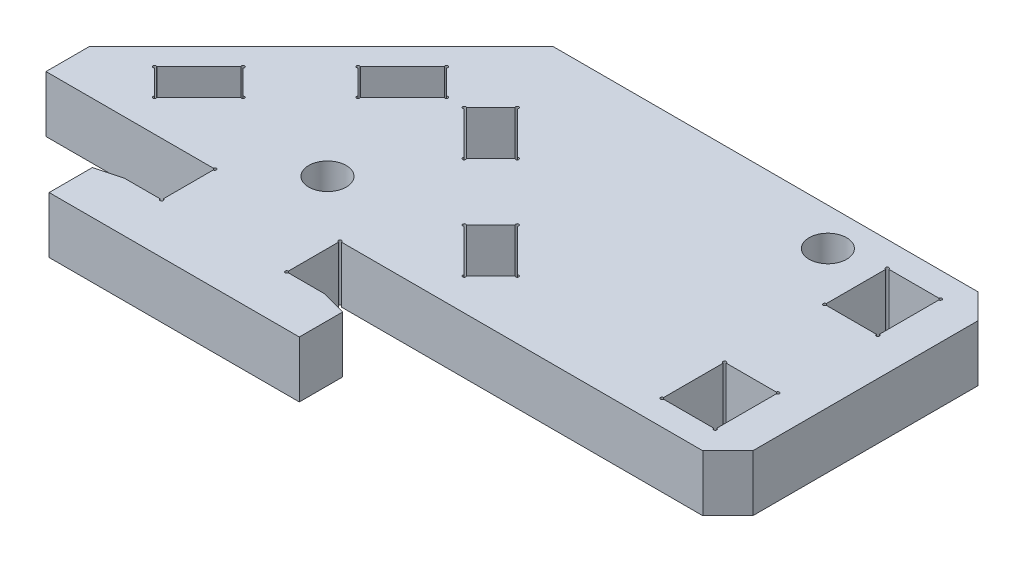
SolidWorks part; units mm, degrees
ref_plane "Front Plane" through (0, 0, 0) normal (0, 0, 1) x (1, 0, 0)
ref_plane "Top Plane" through (0, 0, 0) normal (0, 1, 0) x (1, 0, 0)
ref_plane "Right Plane" through (0, 0, 0) normal (1, 0, 0) x (0, 0, -1)
sketch "Sketch1" plane through (0, 0, 0) normal (0, 1, 0) x (1, 0, 0)
  line L0 (-18.5, -18.5) -> (0, 0)
  line L1 (0, 0) -> (36, 0)
  line L2 (36, 0) -> (36, -22)
  line L3 (36, -22) -> (-18.5, -22)
  line L4 (-18.5, -18.5) -> (-18.5, -22)
  dimension "D1" = 22
  dimension "D2" = 45
  dimension "D3" = 36
  dimension "D4" = 3.5
extrude "Boss-Extrude1" add sketch "Sketch1" along normal blind 4.5
sketch "Sketch2" plane through (0, 4.5, 0) normal (0, 1, 0) x (1, 0, 0)
  line L0 (-6.364, -9.1924) -> (-2.8284, -5.6569)
  line L1 (-6.364, -9.1924) -> (-4.2426, -11.3137)
  line L2 (-2.8284, -5.6569) -> (-0.7071, -7.7782)
  line L3 (-4.2426, -11.3137) -> (-0.7071, -7.7782)
  line L4 (-10.9602, -13.7886) -> (-8.8388, -15.9099)
  line L5 (-10.9602, -13.7886) -> (-14.4957, -17.3241)
  line L6 (-8.8388, -15.9099) -> (-12.3744, -19.4454)
  line L7 (-14.4957, -17.3241) -> (-12.3744, -19.4454)
  line L8 (0, 0) -> (-18.5, -18.5) construction
  line L9 (-2.8284, -5.6569) -> (0, -2.8284) construction
  dimension "D1" = 2
  dimension "D2" = 5
  dimension "D3" = 3
  dimension "D4" = 11.5
  dimension "D5" = 4
extrude "Cut-Extrude1" cut sketch "Sketch2" against normal through all
mirror "Mirror1" about plane through (0, 0, 0) normal (1, 0, 0) of "Cut-Extrude1"
sketch "Sketch3" plane through (0, 4.5, 0) normal (0, 1, 0) x (1, 0, 0)
  line L1 (33, -2) -> (28.75, -2)
  line L2 (33, -2) -> (33, -7)
  line L3 (33, -7) -> (28.75, -7)
  line L4 (28.75, -2) -> (28.75, -7)
  line L5 (33, -15) -> (28.75, -15)
  line L6 (33, -15) -> (33, -20)
  line L7 (33, -20) -> (28.75, -20)
  line L8 (28.75, -15) -> (28.75, -20)
  line L9 (-12.3744, -19.4454) -> (-8.8388, -15.9099) construction
  line L10 (36, 0) -> (0, 0) construction
  line L11 (36, -22) -> (36, 0) construction
  line L12 (-18.5, -22) -> (36, -22) construction
  dimension "D1" = 2
  dimension "D2" = 3
  dimension "D3" = 2
  dimension "D4" = 4.25
extrude "Cut-Extrude2" cut sketch "Sketch3" against normal through all
sketch "Sketch4" plane through (0, 4.5, 0) normal (0, 1, 0) x (1, 0, 0)
  line L0 (36, -22) -> (36, 0) construction
  circle A0 centre (0, -18) radius 1.5
  circle A1 centre (25, -3) radius 1.5
  dimension "D1" = 3
  dimension "D2" = 18
  dimension "D3" = 3
  dimension "D4" = 11
extrude "Cut-Extrude3" cut sketch "Sketch4" against normal through all
sketch "Sketch5" plane through (0, 4.5, 0) normal (0, 1, 0) x (1, 0, 0)
  line L0 (-18.5, -22) -> (36, -22) construction
  line L1 (-5, -22) -> (5, -22)
  line L2 (-5, -22) -> (-5, -26.25)
  line L3 (0, -22) -> (0, 0) construction
  line L4 (5, -22) -> (5, -26.25)
  line L5 (-5, -26.25) -> (-10, -26.25)
  line L6 (10, -30.25) -> (-10, -30.25)
  line L7 (10, -30.25) -> (10, -26.25)
  line L8 (10, -26.25) -> (5, -26.25)
  line L9 (-10, -30.25) -> (-10, -26.25)
  dimension "D1" = 4.25
  dimension "D2" = 10
  dimension "D3" = 20
  dimension "D4" = 4
extrude "Boss-Extrude2" add sketch "Sketch5" against normal up to surface (4.5 mm away) up to face at (25, 0, 4.5)
chamfer "Chamfer1" distance 2 angle 15 2 edges at (10, 2.25, 26.25) (-10, 2.25, 26.25)
sketch "Sketch6" plane through (0, 4.5, 0) normal (0, 1, 0) x (1, 0, 0)
  line L0 (36, 0) -> (0, 0) construction
  line L1 (24.6771, 0) -> (14.6771, 0)
  line L2 (24.6771, 0) -> (24.6771, 4.5)
  line L4 (14.6771, 0) -> (14.6771, 4.5)
  line L5 (24.6771, 4.5) -> (29.6771, 4.5)
  line L6 (9.6771, 8.5) -> (29.6771, 8.5)
  line L7 (9.6771, 8.5) -> (9.6771, 4.5)
  line L8 (9.6771, 4.5) -> (14.6771, 4.5)
  line L9 (29.6771, 8.5) -> (29.6771, 4.5)
  dimension "D1" = 10
  dimension "D2" = 4.5
  dimension "D3" = 4
  dimension "D4" = 20
extrude "Boss-Extrude3" [suppressed] add sketch "Sketch6" against normal up to surface (4.5 mm away)
chamfer "Chamfer2" distance 2 angle 45 2 edges at (36, 2.25, 0) (36, 2.25, 22)
sketch "Sketch7" plane through (0, 4.5, 0) normal (0, 1, 0) x (1, 0, 0)
  point P0 (-12.3744, -19.4454)
  point P1 (-14.4957, -17.3241)
  point P3 (-10.9602, -13.7886)
  point P5 (-8.8388, -15.9099)
  point P7 (-4.2426, -11.3137)
  point P9 (-6.364, -9.1924)
  point P11 (-2.8284, -5.6569)
  point P13 (-0.7071, -7.7782)
  point P15 (0.7071, -7.7782)
  point P17 (2.8284, -5.6569)
  point P19 (6.364, -9.1924)
  point P21 (4.2426, -11.3137)
  point P23 (10.9602, -13.7886)
  point P25 (8.8388, -15.9099)
  point P27 (12.3744, -19.4454)
  point P29 (14.4957, -17.3241)
  point P31 (28.75, -7)
  point P33 (28.75, -2)
  point P35 (33, -2)
  point P37 (33, -7)
  point P39 (33, -15)
  point P41 (28.75, -15)
  point P43 (28.75, -20)
  point P45 (33, -20)
  point P47 (5, -26.25)
  point P49 (-5, -26.25)
  point P51 (-5, -22)
  point P53 (5, -22)
sketch "Sketch8" plane through (0, 4.5, 0) normal (0, 1, 0) x (1, 0, 0)
  circle A0 centre (-12.3744, -19.4454) radius 0.125
  dimension "D1" = 0.25
extrude "Cut-Extrude4" cut sketch "Sketch8" against normal through all
pattern_sketch "Sketch-Pattern1" of "Cut-Extrude4" driven by "Sketch7"
